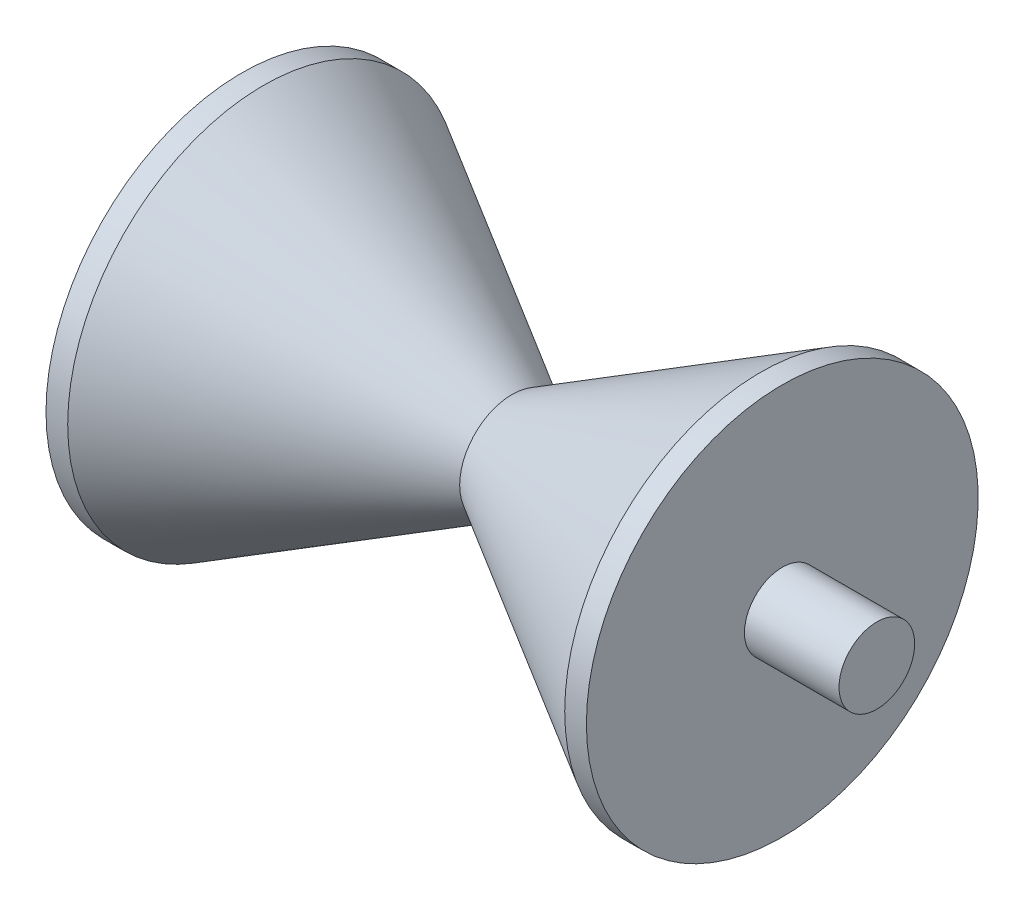
SolidWorks part; units mm, degrees
material "Plain Carbon Steel"
ref_plane "Front Plane" through (0, 0, 0) normal (0, 0, 1) x (1, 0, 0)
ref_plane "Top Plane" through (0, 0, 0) normal (0, 1, 0) x (1, 0, 0)
ref_plane "Right Plane" through (0, 0, 0) normal (1, 0, 0) x (0, 0, -1)
sketch "Sketch1" plane through (0, 0, 0) normal (0, 0, 1) x (1, 0, 0)
  line L0 (-7.6521, 0) -> (15.3332, 0) construction
  line L1 (0, 0) -> (0, 0.7)
  line L2 (0, 0.7) -> (1.75, 0.7)
  line L3 (1.75, 0.7) -> (1.75, 3.625)
  line L4 (1.75, 3.625) -> (2.1514, 3.625)
  line L5 (2.1514, 3.625) -> (6.75, 0.97)
  line L6 (6.75, 0.97) -> (11.3486, 3.625)
  line L7 (11.3486, 3.625) -> (11.75, 3.625)
  line L8 (11.75, 3.625) -> (11.75, 0.7)
  line L9 (11.75, 0.7) -> (13.5, 0.7)
  line L10 (13.5, 0.7) -> (13.5, 0)
  line L11 (6.75, -3.5804) -> (6.75, 5.7363) construction
  line L12 (0, 0) -> (13.5, 0)
  dimension "D1" = 1.75
  dimension "D2" = 10
  dimension "D3" = 0.7
  dimension "D4" = 0.97
  dimension "D5" = 3.625
  dimension "D6" = 60
revolve "Revolve1" add sketch "Sketch1" angle 360 about L12
